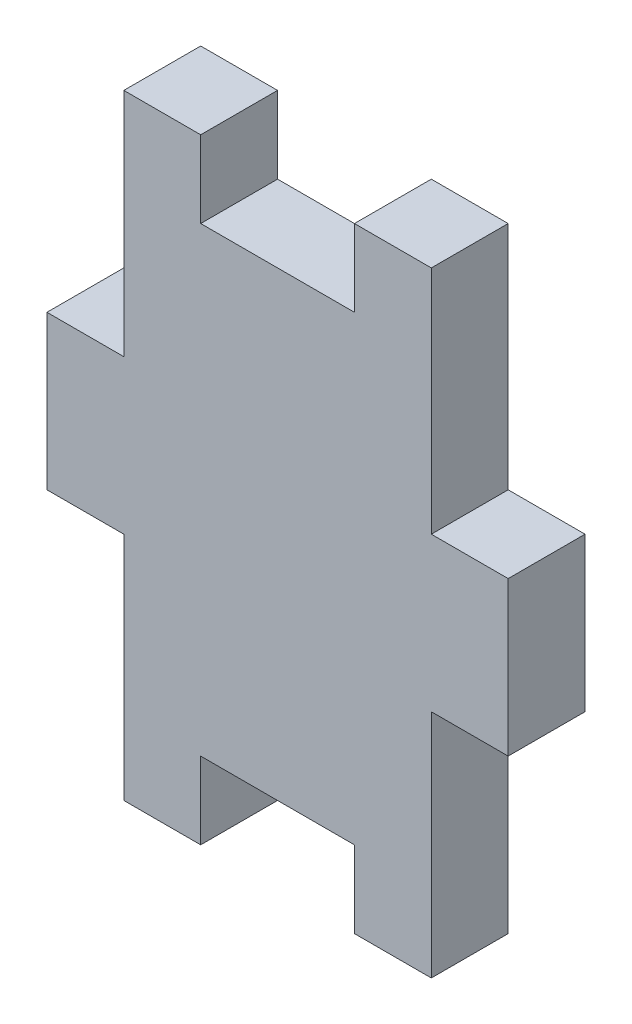
SolidWorks part; units mm, degrees
ref_plane "Front Plane" through (0, 0, 0) normal (0, 0, 1) x (1, 0, 0)
ref_plane "Top Plane" through (0, 0, 0) normal (0, 1, 0) x (1, 0, 0)
ref_plane "Right Plane" through (0, 0, 0) normal (1, 0, 0) x (0, 0, -1)
sketch "Sketch1" plane through (0, 0, 0) normal (0, 0, 1) x (1, 0, 0)
  line L0 (0, -9.525) -> (0, 9.525) construction
  line L1 (-6.35, 12.7) -> (-3.175, 12.7)
  line L2 (-6.35, 12.7) -> (-6.35, 3.175)
  line L3 (0, 0) -> (35.3222, 0) construction
  line L4 (9.525, 3.175) -> (9.525, -3.175)
  line L5 (6.35, 3.175) -> (9.525, 3.175)
  line L6 (3.175, -9.525) -> (3.175, -12.7)
  line L7 (-3.175, -9.525) -> (3.175, -9.525)
  line L8 (-3.175, -12.7) -> (-3.175, -9.525)
  line L9 (6.35, 12.7) -> (6.35, 3.175)
  line L10 (6.35, 12.7) -> (3.175, 12.7)
  line L11 (-6.35, 3.175) -> (-9.525, 3.175)
  line L12 (-6.35, -3.175) -> (-9.525, -3.175)
  line L13 (6.35, -12.7) -> (3.175, -12.7)
  line L14 (-9.525, 3.175) -> (-9.525, -3.175)
  line L15 (6.35, -12.7) -> (6.35, -3.175)
  line L19 (6.35, -3.175) -> (9.525, -3.175)
  line L20 (-6.35, -12.7) -> (-6.35, -3.175)
  line L21 (-6.35, -12.7) -> (-3.175, -12.7)
  line L22 (-3.175, 12.7) -> (-3.175, 9.525)
  line L23 (-3.175, 9.525) -> (3.175, 9.525)
  line L24 (3.175, 9.525) -> (3.175, 12.7)
  point P18 (-9.525, 0)
  point P26 (9.525, 0)
  dimension "D1" = 3.175
  dimension "D2" = 19.05
  dimension "D3" = 6.35
  dimension "D4" = 25.4
  dimension "D5" = 3.175
  dimension "D6" = 3.175
extrude "Extrude1" add sketch "Sketch1" along normal blind 3.175
